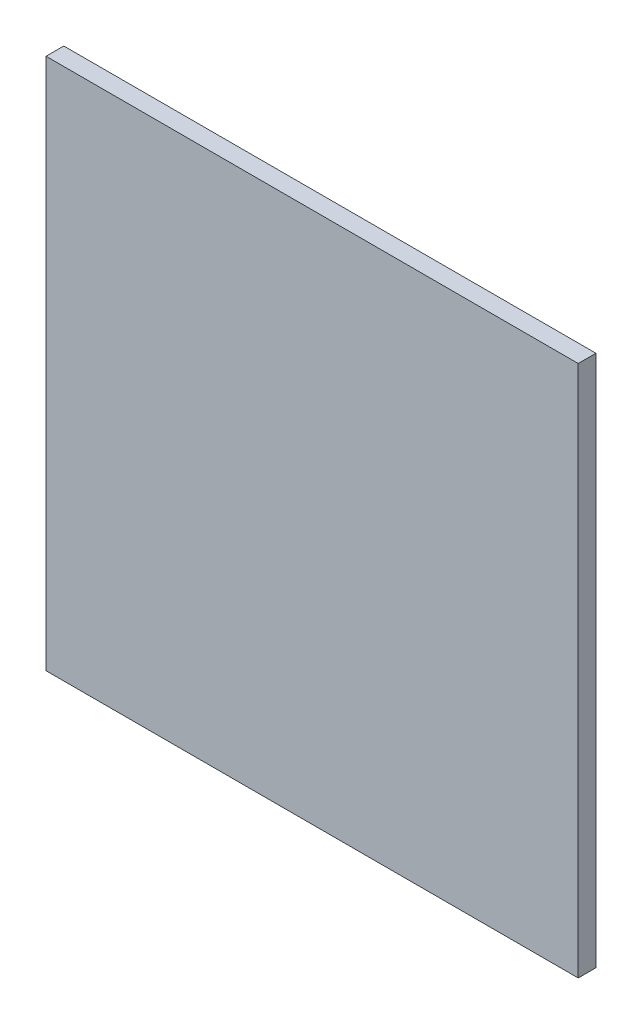
SolidWorks part; units mm, degrees
material "ABS"
ref_plane "Plano frontal" through (0, 0, 0) normal (0, 0, 1) x (1, 0, 0)
ref_plane "Plano superior" through (0, 0, 0) normal (0, 1, 0) x (1, 0, 0)
ref_plane "Plano direito" through (0, 0, 0) normal (1, 0, 0) x (0, 0, -1)
sketch "Esboço1" plane through (0, 0, 0) normal (0, 0, 1) x (1, 0, 0)
  line L1 (-81.3088, 12.9223) -> (218.6912, 12.9223)
  line L2 (-81.3088, 12.9223) -> (-81.3088, -287.0777)
  line L3 (-81.3088, -287.0777) -> (218.6912, -287.0777)
  line L4 (218.6912, 12.9223) -> (218.6912, -287.0777)
  dimension "D1" = 300
  dimension "D2" = 300
extrude "Ressalto-extrusão1" add sketch "Esboço1" along normal blind 10
